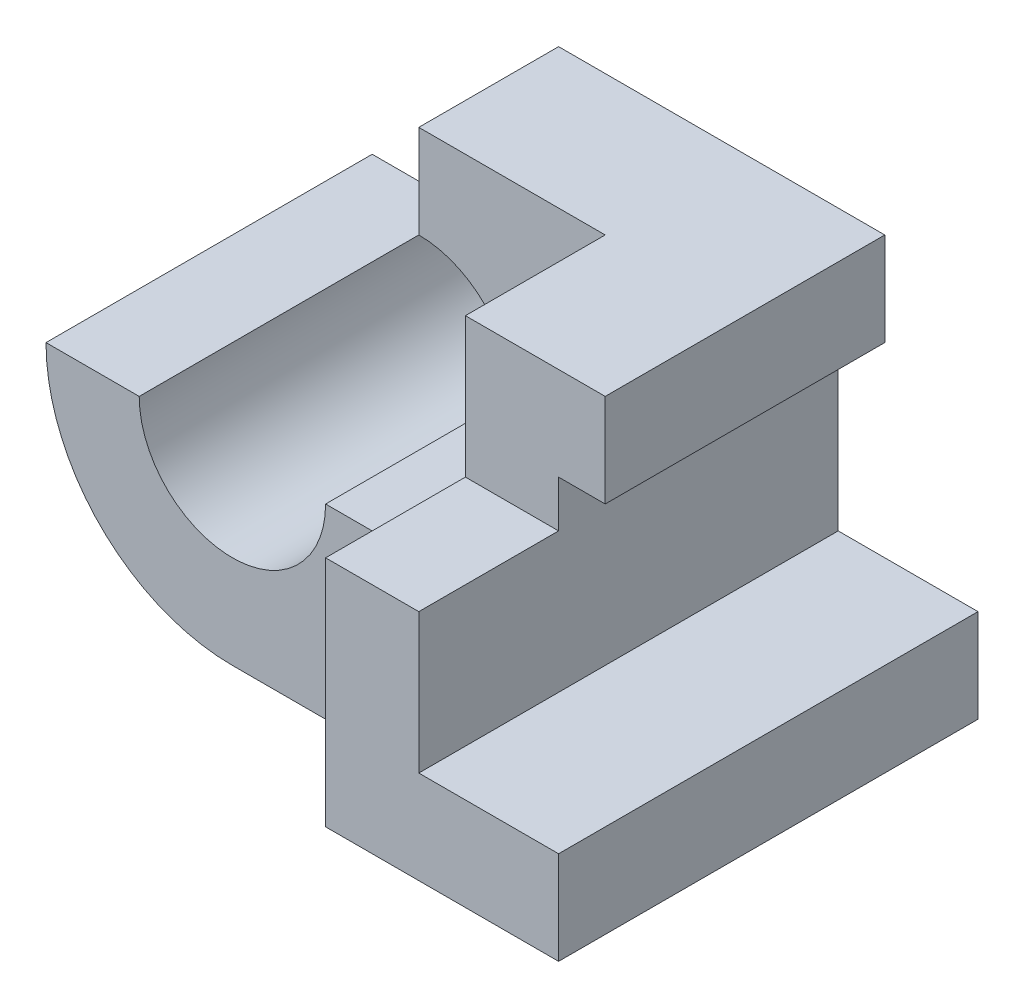
SolidWorks part; units mm, degrees
ref_plane "Front Plane" through (0, 0, 0) normal (0, 0, 1) x (1, 0, 0)
ref_plane "Top Plane" through (0, 0, 0) normal (0, 1, 0) x (1, 0, 0)
ref_plane "Right Plane" through (0, 0, 0) normal (1, 0, 0) x (0, 0, -1)
sketch "Sketch1" plane through (0, 0, 0) normal (0, 0, 1) x (1, 0, 0)
  line L0 (0, 40) -> (0, 20)
  line L1 (-40, 0) -> (-20, 0)
  line L2 (0, 40) -> (70, 40)
  line L3 (70, 40) -> (70, -40)
  line L4 (70, -40) -> (0, -40)
  circle A0 centre (0, 0) radius 20
  arc A1 (0, 40) -> (-40, 0) centre (0, 0) cw
  dimension "D1" = 40
  dimension "D2" = 20
  dimension "D3" = 70
extrude "Boss-Extrude1" add sketch "Sketch1" along normal blind 90 contours A1 L0 A0 L1 | L2 A1 L4 L3
sketch "Sketch2" plane through (0, 0, 90) normal (0, 0, 1) x (1, 0, 0)
  line L0 (70, 40) -> (70, -40) construction
  line L1 (70, 20) -> (40, 20)
  line L2 (70, 20) -> (70, -20)
  line L3 (70, -20) -> (40, -20)
  line L4 (40, 20) -> (40, -20)
  dimension "D1" = 30
  dimension "D2" = 20
  dimension "D3" = 40
extrude "Cut-Extrude1" cut sketch "Sketch2" against normal blind 90
sketch "Sketch3" plane through (0, 0, 90) normal (0, 0, 1) x (1, 0, 0)
  line L0 (70, 20) -> (40, 20) construction
  line L1 (70, 20) -> (50, 20)
  line L2 (70, 20) -> (70, 40)
  line L3 (70, 40) -> (50, 40)
  line L4 (50, 20) -> (50, 40)
  line L5 (70, 40) -> (70, 20) construction
  line L6 (0, 40) -> (70, 40) construction
  dimension "D1" = 20
extrude "Cut-Extrude2" cut sketch "Sketch3" against normal blind 90
ref_plane "Plane1" through (0, -40, 0) normal (0, 1, 0) x (1, 0, 0)
sketch "Sketch4" plane through (0, -40, 0) normal (0, 1, 0) x (1, 0, 0)
  line L0 (-40, -90) -> (-20, -90) construction
  line L1 (-40, -90) -> (40, -90)
  line L2 (-40, -90) -> (-40, -70)
  line L3 (-40, -70) -> (40, -70)
  line L4 (40, -90) -> (40, -70)
  dimension "D1" = 0
  dimension "D2" = 20
  dimension "D3" = 0
  dimension "D4" = 80
extrude "Cut-Extrude3" cut sketch "Sketch4" along normal blind 90
sketch "Sketch5" plane through (0, 0, 0) normal (1, 0, 0) x (0, 0, -1)
  line L0 (-70, 40) -> (-70, 20) construction
  line L1 (-100, 40) -> (-70, 40)
  line L2 (-100, 40) -> (-100, 10)
  line L3 (-100, 10) -> (-70, 10)
  line L4 (-70, 40) -> (-70, 10)
  point P4 (-70, 30)
  dimension "D1" = 30
  dimension "D2" = 30
  dimension "D3" = 0
  dimension "D4" = 0
extrude "Cut-Extrude4" cut sketch "Sketch5" along normal blind 90
sketch "Sketch7" plane through (0, 0, 70) normal (0, 0, 1) x (1, 0, 0)
  line L0 (0, 40) -> (0, 20) construction
  line L1 (20, 0) -> (40, 0)
  line L2 (0, 20) -> (0, 40)
  line L3 (0, 40) -> (40, 40)
  line L4 (0, 40) -> (50, 40) construction
  line L5 (40, 40) -> (40, 0)
  arc A0 (0, 20) -> (20, 0) centre (0, 0) cw
  arc A1 (-20, 0) -> (0, 20) centre (0, 0) ccw construction
  dimension "D1" = 20
  dimension "D2" = 40
extrude "Cut-Extrude6" cut sketch "Sketch7" against normal blind 40
ref_plane "Plane2" through (70, 0, 0) normal (1, 0, 0) x (0, 0, -1)
sketch "Sketch10" plane through (70, 0, 0) normal (1, 0, 0) x (0, 0, -1)
  line L0 (-70, 10) -> (-70, 20)
  line L1 (-90, -20) -> (-37.0894, -20)
  line L2 (-90, -20) -> (-90, 10)
  line L3 (-90, 10) -> (-37.0894, 10)
  line L5 (-70, 20) -> (-21.4218, 20)
  line L6 (-21.4218, 20) -> (-21.4218, -20)
  line L7 (0, -20) -> (-90, -20) construction
  line L8 (-21.4218, -20) -> (-90, -20)
  dimension "D1" = 30
  dimension "D2" = 20
  dimension "D3" = 10
extrude "Boss-Extrude6" add sketch "Sketch10" against normal blind 30
sketch "Sketch11" plane through (70, 0, 0) normal (1, 0, 0) x (0, 0, -1)
  line L0 (-21.4218, -20) -> (-70, -20)
  line L1 (-70, -20) -> (-70, 10)
  line L2 (-70, 10) -> (-70, 20)
  line L3 (-70, 20) -> (-21.4218, 20)
  line L4 (-70, 20) -> (-21.4218, 20) construction
  line L5 (-21.4218, 20) -> (-21.4218, -20)
extrude "Cut-Extrude7" cut sketch "Sketch11" against normal blind 20
sketch "Sketch12" plane through (50, 0, 0) normal (1, 0, 0) x (0, 0, -1)
  line L1 (-70, 40) -> (-60, 40)
  line L2 (-70, 40) -> (-70, 10)
  line L3 (-70, 10) -> (-60, 10)
  line L4 (-60, 40) -> (-60, 10)
  dimension "D1" = 30
  dimension "D2" = 10
extrude "Cut-Extrude8" cut sketch "Sketch12" against normal blind 20
sketch "Sketch13" plane through (0, 0, 70) normal (0, 0, -1) x (-1, 0, 0)
  line L0 (-50, 10) -> (-70, 10) construction
  line L1 (-50, -20) -> (-70, -20)
  line L2 (-50, -20) -> (-50, 10)
  line L3 (-50, 10) -> (-70, 10)
  line L4 (-70, -20) -> (-70, 10)
  dimension "D1" = 20
extrude "Cut-Extrude9" cut sketch "Sketch13" against normal blind 20
sketch "Sketch14" plane through (40, 0, 0) normal (1, 0, 0) x (0, 0, -1)
  line L1 (-21.4218, 20) -> (0, 20)
  line L2 (-21.4218, 20) -> (-21.4218, -20)
  line L3 (-21.4218, -20) -> (0, -20)
  line L4 (0, 20) -> (0, -20)
extrude "Boss-Extrude7" add sketch "Sketch14" along normal blind 10
ref_plane "Plane3" through (0, 40, 0) normal (0, 1, 0) x (1, 0, 0)
sketch "Sketch16" plane through (0, 40, 0) normal (0, 1, 0) x (1, 0, 0)
  line L0 (50, -60) -> (70, -60)
  line L1 (50, 0) -> (70, 0)
  line L2 (70, 0) -> (70, -60)
  line L9 (40, -60) -> (50, -60)
  line L10 (50, -60) -> (50, 0)
  line L11 (50, 0) -> (0, 0)
  line L12 (0, 0) -> (0, -30)
  line L13 (0, -30) -> (40, -30)
  line L14 (40, -30) -> (40, -60)
  line L16 (50, -60) -> (50, 0)
  dimension "D1" = 20
  dimension "D2" = 0
extrude "Boss-Extrude8" add sketch "Sketch16" against normal blind 30
sketch "Sketch17" plane through (70, 0, 0) normal (1, 0, 0) x (0, 0, -1)
  line L0 (-60, 40) -> (0, 40) construction
  line L1 (0, 10) -> (-30, 10)
  line L2 (0, 10) -> (0, 40)
  line L3 (0, 40) -> (-30, 40)
  line L4 (-30, 10) -> (-30, 40)
  dimension "D1" = 30
extrude "Cut-Extrude10" cut sketch "Sketch17" against normal blind 20
sketch "Sketch18" plane through (50, 0, 0) normal (1, 0, 0) x (0, 0, -1)
  line L1 (-90, 10) -> (0, 10)
  line L2 (-90, 10) -> (-90, -20)
  line L3 (-90, -20) -> (0, -20)
  line L4 (0, 10) -> (0, -20)
extrude "Boss-Extrude9" add sketch "Sketch18" along normal blind 10
sketch "Sketch19" plane through (70, 0, 0) normal (1, 0, 0) x (0, 0, -1)
  line L1 (-90, -20) -> (0, -20)
  line L2 (-90, -20) -> (-90, -40)
  line L3 (-90, -40) -> (0, -40)
  line L4 (0, -20) -> (0, -40)
extrude "Boss-Extrude10" add sketch "Sketch19" along normal blind 20
sketch "Sketch21" plane through (0, 0, 30) normal (0, 0, -1) x (-1, 0, 0)
  line L0 (-50, 10) -> (-60, 10) construction
  line L1 (-70, 40) -> (-59.9999, 40)
  line L2 (-70, 40) -> (-70, 10)
  line L3 (-70, 10) -> (-59.9999, 10)
  line L4 (-59.9999, 40) -> (-59.9999, 10)
  dimension "D1" = 10.0001
extrude "Boss-Extrude13" add sketch "Sketch21" along normal blind 30
sketch "Sketch22" plane through (0, 10, 0) normal (0, -1, 0) x (1, 0, 0)
  line L0 (70, 60) -> (70, 0) construction
  line L1 (60, 0) -> (70, 0)
  line L2 (60, 0) -> (60, 30)
  line L3 (60, 30) -> (70, 30)
  line L4 (70, 0) -> (70, 30)
  dimension "D1" = 30
extrude "Cut-Extrude13" cut sketch "Sketch22" against normal blind 29.999
sketch "Sketch23" plane through (60, 0, 0) normal (1, 0, 0) x (0, 0, -1)
  line L1 (-30, 39.999) -> (0, 39.999)
  line L2 (-30, 39.999) -> (-30, 10)
  line L3 (-30, 10) -> (0, 10)
  line L4 (0, 39.999) -> (0, 10)
extrude "Cut-Extrude14" cut sketch "Sketch23" against normal blind 1
sketch "Sketch24" plane through (0, 39.999, 0) normal (0, -1, 0) x (1, 0, 0)
  line L1 (59.9999, 30) -> (70, 30)
  line L2 (59.9999, 30) -> (59.9999, 0)
  line L3 (59.9999, 0) -> (70, 0)
  line L4 (70, 30) -> (70, 0)
extrude "Cut-Extrude15" cut sketch "Sketch24" against normal blind 1
sketch "Sketch25" plane through (0, 10, 0) normal (0, 1, 0) x (1, 0, 0)
  line L1 (50, 0) -> (60, 0)
  line L2 (50, 0) -> (50, -30)
  line L3 (50, -30) -> (60, -30)
  line L4 (60, 0) -> (60, -30)
extrude "Cut-Extrude16" cut sketch "Sketch25" against normal blind 10
sketch "Sketch27" plane through (0, 0, 60) normal (0, 0, 1) x (1, 0, 0)
  line L1 (70, 10) -> (60, 10)
  line L2 (70, 10) -> (70, 20)
  line L3 (70, 20) -> (60, 20)
  line L4 (60, 10) -> (60, 20)
  dimension "D1" = 10
  dimension "D2" = 10
extrude "Cut-Extrude18" cut sketch "Sketch27" against normal blind 30
sketch "Sketch30" plane through (0, 0, 30) normal (0, 0, -1) x (-1, 0, 0)
  line L0 (-50, 40) -> (-50, 0) construction
  line L1 (-70, 40) -> (-50, 40)
  line L2 (-70, 40) -> (-70, 20)
  line L3 (-70, 20) -> (-50, 20)
  line L4 (-50, 40) -> (-50, 20)
extrude "Boss-Extrude16" add sketch "Sketch30" along normal blind 30
sketch "Sketch31" plane through (50, 0, 0) normal (1, 0, 0) x (0, 0, -1)
  line L1 (-30, 20) -> (0, 20)
  line L2 (-30, 20) -> (-30, 0)
  line L3 (-30, 0) -> (0, 0)
  line L4 (0, 20) -> (0, 0)
extrude "Boss-Extrude17" add sketch "Sketch31" along normal blind 10
